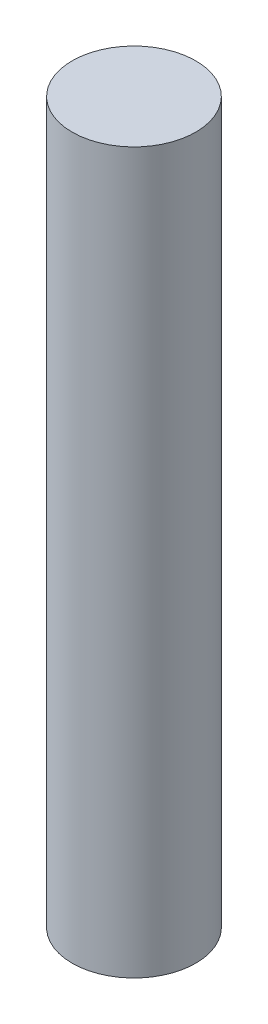
SolidWorks part; units mm, degrees
ref_plane "Front Plane" through (0, 0, 0) normal (0, 0, 1) x (1, 0, 0)
ref_plane "Top Plane" through (0, 0, 0) normal (0, 1, 0) x (1, 0, 0)
ref_plane "Right Plane" through (0, 0, 0) normal (1, 0, 0) x (0, 0, -1)
sketch "Sketch1" plane through (0, 0, 0) normal (0, 1, 0) x (1, 0, 0)
  circle A0 centre (0, 0) radius 3.6805
extrude "Boss-Extrude1" add sketch "Sketch1" along normal blind 42.8625
